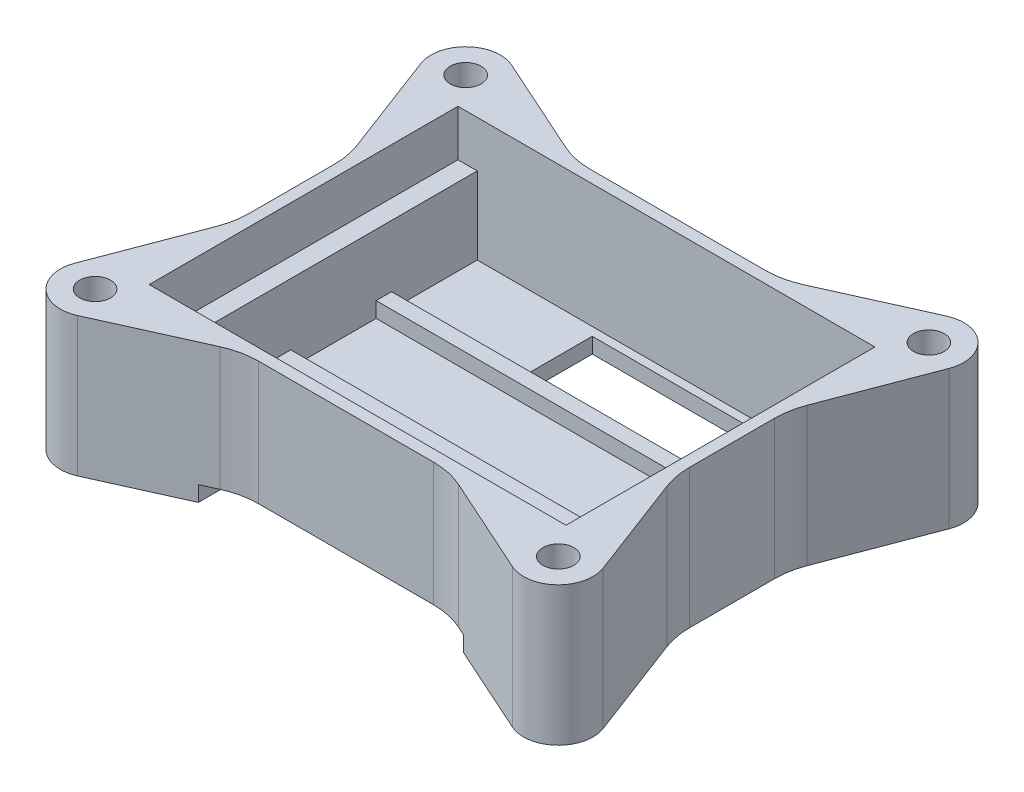
SolidWorks part; units mm, degrees
ref_plane "Front Plane" through (0, 0, 0) normal (0, 0, 1) x (1, 0, 0)
ref_plane "Top Plane" through (0, 0, 0) normal (0, 1, 0) x (1, 0, 0)
ref_plane "Right Plane" through (0, 0, 0) normal (1, 0, 0) x (0, 0, -1)
sketch "Sketch1" plane through (0, 0, 0) normal (0, 1, 0) x (1, 0, 0)
  line L0 (0, 20) -> (0, -20) construction
  line L1 (-28.5, 21.5) -> (28.5, 21.5)
  line L2 (-28.5, 21.5) -> (-28.5, -21.5)
  line L3 (-28.5, -21.5) -> (28.5, -21.5)
  line L4 (28.5, 21.5) -> (28.5, -21.5)
  line L5 (-27, 20) -> (27, 20)
  line L6 (-27, 20) -> (-27, -20)
  line L7 (-27, -20) -> (27, -20)
  line L8 (27, 20) -> (27, -20)
  line L9 (-30, 24) -> (30, 24) construction
  line L10 (-30, 24) -> (-30, -24) construction
  line L11 (-30, -24) -> (30, -24) construction
  line L12 (30, 24) -> (30, -24) construction
  line L13 (0, 20) -> (0, 21.5) construction
  line L14 (0, 21.5) -> (0, 24) construction
  line L15 (0, -20) -> (0, -21.5) construction
  line L16 (0, -21.5) -> (0, -24) construction
  line L17 (-28.5, 0) -> (-27, 0) construction
  line L18 (28.1534, 28.1037) -> (13.4782, 21.5)
  line L19 (34.2075, 22.404) -> (28.5, 7.3575)
  line L20 (-34.2075, 22.404) -> (-28.5, 7.3575)
  line L21 (-28.1534, 28.1037) -> (-13.4782, 21.5)
  line L22 (-34.2075, -22.404) -> (-28.5, -7.3575)
  line L23 (-28.1534, -28.1037) -> (-13.4782, -21.5)
  line L24 (13.4782, -21.5) -> (28.1534, -28.1037)
  line L25 (28.5, -7.3575) -> (34.2075, -22.404)
  arc A0 (-28.1534, 28.1037) -> (-34.2075, 22.404) centre (-30, 24) ccw
  circle A1 centre (-30, 24) radius 2
  arc A2 (-34.2075, -22.404) -> (-28.1534, -28.1037) centre (-30, -24) ccw
  circle A3 centre (-30, -24) radius 2
  arc A4 (28.1534, -28.1037) -> (34.2075, -22.404) centre (30, -24) ccw
  circle A5 centre (30, -24) radius 2
  arc A6 (34.2075, 22.404) -> (28.1534, 28.1037) centre (30, 24) ccw
  circle A7 centre (30, 24) radius 2
  dimension "D4" = 4
  dimension "D5" = 2.5
  dimension "D1" = 54
  dimension "D2" = 40
  dimension "D3" = 1.5
  dimension "D6" = 45
  dimension "D7" = 45
  dimension "D8" = 60
  dimension "D9" = 48
  dimension "D10" = 45
  dimension "D11" = 45
  dimension "D12" = 43
  dimension "D13" = 57
extrude "Boss-Extrude1" add sketch "Sketch1" along normal blind 18 contours L21 A0 L20 L2 L1 A1 | L22 A2 L23 L3 L2 A3 | L4 L1 L2 L3 L5 L8 L7 L6 | L24 A4 L25 L4 L3 A5 | L19 A6 L18 L1 L4 A7
sketch "Sketch2" plane through (0, 0, 0) normal (0, 1, 0) x (1, 0, 0)
  line L0 (-27, -20) -> (27, -20) construction
  line L1 (-27, 20) -> (-24.5, 20)
  line L2 (-27, 20) -> (-27, -20)
  line L3 (-27, -20) -> (-24.5, -20)
  line L4 (-24.5, 20) -> (-24.5, -20)
  line L6 (27, 20) -> (23, 20)
  line L7 (27, 20) -> (27, -20)
  line L8 (27, -20) -> (23, -20)
  line L9 (23, 20) -> (23, -20)
  dimension "D1" = 2.5
  dimension "D2" = 4
extrude "Boss-Extrude2" add sketch "Sketch2" along normal offset from surface (12 mm away) 6 contours L4 L3 L2 L1
sketch "Sketch3" plane through (0, 0, 0) normal (0, 1, 0) x (1, 0, 0)
  line L0 (-0.75, 19.15) -> (-0.75, 20) construction
  line L1 (-25.875, 19.15) -> (25.875, 19.15) construction
  line L2 (-25.875, 19.15) -> (-25.875, -19.15) construction
  line L3 (-25.875, -19.15) -> (25.875, -19.15) construction
  line L4 (25.875, 19.15) -> (25.875, -19.15) construction
  line L5 (-24.5, 20) -> (23, 20) construction
  line L6 (-0.75, -19.15) -> (-0.75, -20) construction
  line L7 (-24.5, -20) -> (23, -20) construction
  line L8 (-27, 0) -> (-25.875, 0) construction
  line L9 (27, 0) -> (25.875, 0) construction
  line L10 (-27, 20) -> (-27, -20) construction
  line L11 (27, -20) -> (27, 20) construction
  line L12 (23, 20) -> (23, -20) construction
  line L13 (-20.375, -7.65) -> (19.625, -7.65)
  line L14 (-20.375, -7.65) -> (-20.375, -16.15)
  line L15 (-20.375, -16.15) -> (19.625, -16.15)
  line L16 (19.625, -7.65) -> (19.625, -16.15)
  line L17 (-8.5, 18.9) -> (14.5, 18.9)
  line L18 (-8.5, 18.9) -> (-8.5, 10.4)
  line L19 (-8.5, 10.4) -> (14.5, 10.4)
  line L20 (14.5, 18.9) -> (14.5, 10.4)
  line L21 (15.75, 18.9) -> (19.25, 18.9)
  line L22 (15.75, 18.9) -> (15.75, 10.4)
  line L23 (15.75, 10.4) -> (19.25, 10.4)
  line L24 (19.25, 18.9) -> (19.25, 10.4)
  line L25 (-27, 20) -> (27, 20)
  line L26 (-27, 20) -> (-27, -20)
  line L27 (-27, -20) -> (27, -20)
  line L28 (27, 20) -> (27, -20)
  dimension "D1" = 51.75
  dimension "D2" = 38.3
  dimension "D3" = 40
  dimension "D4" = 8.5
  dimension "D5" = 8.5
  dimension "D6" = 3.5
  dimension "D7" = 23
  dimension "D8" = 1.25
  dimension "D9" = 3.75
  dimension "D10" = 0.25
  dimension "D11" = 3
  dimension "D12" = 5.5
extrude "Boss-Extrude3" add sketch "Sketch3" along normal offset from surface (2 mm away) 10 contours L25 L28 L27 L26
sketch "Sketch4" plane through (0, 0, 0) normal (0, -1, 0) x (1, 0, 0)
  line L0 (-10, -17.9) -> (-10, -19.4)
  line L1 (-10, -19.4) -> (-12, -19.4)
  line L2 (-12, -19.4) -> (-12, -21.4)
  line L3 (-12, -21.4) -> (-13.5, -21.4)
  line L4 (-13.5, -21.4) -> (-13.5, -19.4)
  line L5 (-13.5, -19.4) -> (-15.5, -19.4)
  line L6 (-15.5, -19.4) -> (-15.5, -17.9)
  line L7 (-15.5, -17.9) -> (-13.5, -17.9)
  line L8 (-13.5, -17.9) -> (-13.5, -15.9)
  line L9 (-13.5, -15.9) -> (-12, -15.9)
  line L10 (-12, -15.9) -> (-12, -17.9)
  line L11 (-12, -17.9) -> (-10, -17.9)
  line L12 (-8.5, -18.9) -> (-8.5, -10.4) construction
  line L13 (-12, -8.4) -> (-13.5, -8.4)
  line L14 (-12, -8.4) -> (-12, -13.4)
  line L15 (-12, -13.4) -> (-13.5, -13.4)
  line L16 (-13.5, -8.4) -> (-13.5, -13.4)
  line L17 (-12.75, -13.4) -> (-12.75, -15.9) construction
  line L18 (-12.75, -14.65) -> (-8.5, -14.65) construction
  dimension "D1" = 1.5
  dimension "D2" = 2
  dimension "D3" = 5
  dimension "D4" = 2.5
  dimension "D5" = 1.5
extrude "Cut-Extrude1" cut sketch "Sketch4" against normal blind 1
sketch "Sketch5" plane through (23, 0, 0) normal (-1, 0, 0) x (0, 0, 1)
  line L0 (-20, 2) -> (20, 2) construction
  line L1 (4.15, 2) -> (6.15, 2)
  line L2 (4.15, 2) -> (4.15, 4)
  line L3 (4.15, 4) -> (6.15, 4)
  line L4 (6.15, 2) -> (6.15, 4)
  line L5 (-10.4, 2) -> (-8.9, 2) construction
  line L6 (-8.9, 2) -> (-6.9, 2)
  line L7 (-8.9, 2) -> (-8.9, 4)
  line L8 (-8.9, 4) -> (-6.9, 4)
  line L9 (-6.9, 2) -> (-6.9, 4)
  line L10 (6.15, 2) -> (7.65, 2) construction
  dimension "D1" = 1.5
  dimension "D2" = 3.5
  dimension "D3" = 2
  dimension "D4" = 2
extrude "Boss-Extrude4" add sketch "Sketch5" along normal up to next contours L9 L8 L7 L6
fillet "Fillet1" radius 10 8 edges at (-13.4782, 9, -21.5) (13.4782, 9, -21.5) (28.5, 9, -7.3575) (28.5, 9, 7.3575) (13.4782, 9, 21.5) (-13.4782, 9, 21.5) (-28.5, 9, 7.3575) (-28.5, 9, -7.3575)
sketch "Sketch6" plane through (0, 0, 21.5) normal (0, 0, 1) x (1, 0, 0)
  line L0 (16.625, 0) -> (19.625, 0) construction
  line L1 (16.625, 0) -> (-17.375, 0)
  line L2 (16.625, 0) -> (16.625, 2)
  line L3 (16.625, 2) -> (-17.375, 2)
  line L4 (-17.375, 0) -> (-17.375, 2)
  line L5 (-17.375, 0) -> (-20.375, 0) construction
  line L6 (23, 12) -> (16.625, 12) construction
  line L7 (16.625, 12) -> (16.625, 2) construction
  dimension "D1" = 34
  dimension "D2" = 10
  dimension "D3" = 2
extrude "Cut-Extrude2" cut sketch "Sketch6" against normal up to next and the other way up to next contours L3 L4 L1 L2
